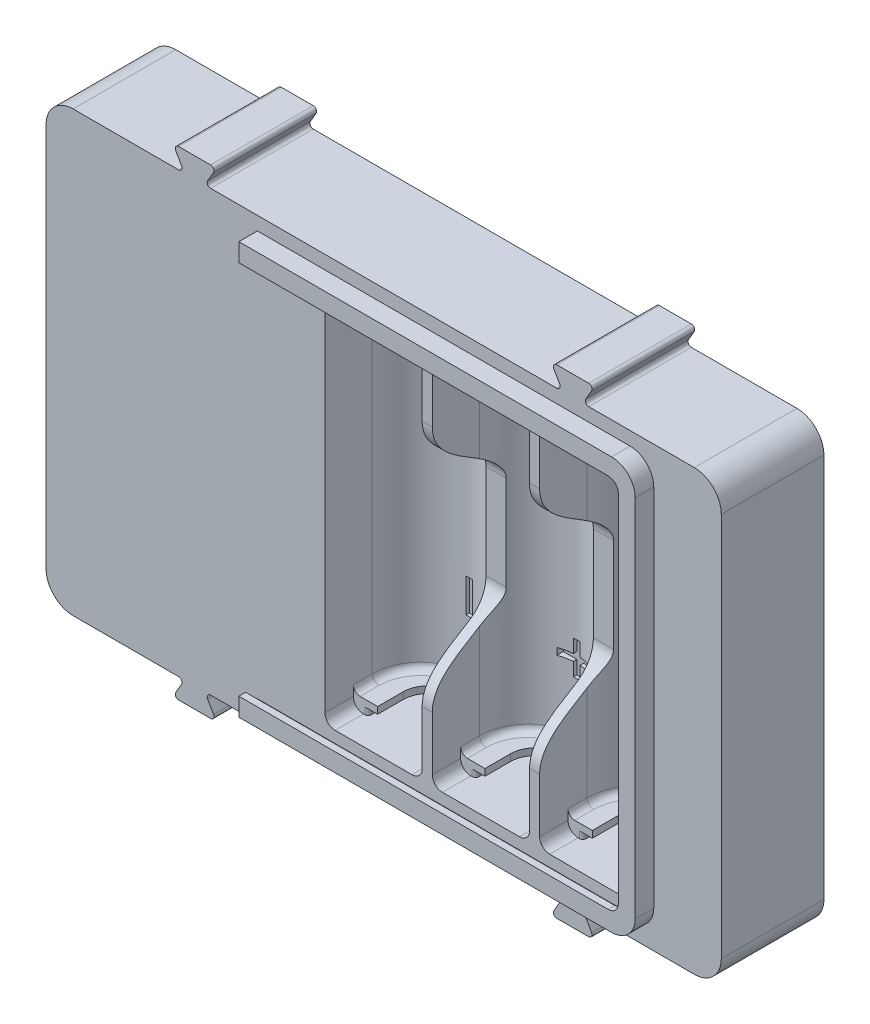
SolidWorks part; units mm, degrees
material "ABS"
ref_plane "Front Plane" through (0, 0, 0) normal (0, 0, 1) x (1, 0, 0)
ref_plane "Top Plane" through (0, 0, 0) normal (0, 1, 0) x (1, 0, 0)
ref_plane "Right Plane" through (0, 0, 0) normal (1, 0, 0) x (0, 0, -1)
sketch "Sketch1" plane through (0, 0, 0) normal (0, 1, 0) x (1, 0, 0)
  line L0 (-24.6, 0) -> (24.6, 0)
  line L1 (0, 0) -> (0, -8.2) construction
  line L2 (-5.4908, -1) -> (5.6475, -1) construction
  line L3 (7, -12.213) -> (7, -2.6204) construction
  line L4 (8.9, -12.0066) -> (8.9, -2.0587) construction
  line L5 (0, -8.2) -> (15.9, -8.2) construction
  line L6 (7.2, -8.2) -> (7.2, -15.2)
  line L7 (8.7, -8.2) -> (8.7, -15.2)
  line L8 (8.7, -15.2) -> (23.1, -15.2) construction
  line L9 (8.7, -15.2) -> (7.2, -15.2)
  line L10 (-1.7094, -15.2) -> (7.2, -15.2) construction
  line L11 (15.9, -8.2) -> (23.1, -8.2) construction
  line L12 (23.1, -15.2) -> (23.1, -8.2)
  line L13 (23.1, -15.2) -> (24.6, -15.2)
  line L14 (24.6, -15.2) -> (24.6, 0)
  line L15 (-24.6, -15.2) -> (-24.6, 0)
  line L16 (-23.1, -15.2) -> (-24.6, -15.2)
  line L17 (-23.1, -15.2) -> (-23.1, -8.2)
  line L18 (-8.7, -8.2) -> (-8.7, -15.2)
  line L19 (-8.7, -15.2) -> (-7.2, -15.2)
  line L20 (-7.2, -8.2) -> (-7.2, -15.2)
  circle A0 centre (0, -8.2) radius 7 construction
  arc A1 (-7.2, -8.2) -> (7.2, -8.2) centre (0, -8.2) cw
  circle A2 centre (15.9, -8.2) radius 7 construction
  arc A3 (8.7, -8.2) -> (23.1, -8.2) centre (15.9, -8.2) cw
  arc A4 (-8.7, -8.2) -> (-23.1, -8.2) centre (-15.9, -8.2) ccw
  dimension "D1" = 14
  dimension "D2" = 0.2
  dimension "D3" = 1
  dimension "D4" = 1.5
  dimension "D5" = 15.2
  dimension "D6" = 15.9
extrude "Boss-Extrude1" add sketch "Sketch1" along normal blind 27.8
sketch "Sketch2" plane through (0, 27.8, 0) normal (0, -1, 0) x (1, 0, 0)
  line L1 (-24.6, 15.2) -> (24.6, 15.2)
  line L2 (-24.6, 15.2) -> (-24.6, 0)
  line L3 (-24.6, 0) -> (24.6, 0)
  line L4 (24.6, 15.2) -> (24.6, 0)
extrude "Boss-Extrude2" add sketch "Sketch2" against normal blind 1.5
ref_plane "Plane1" through (-15.9, 0, 0) normal (1, 0, 0) x (0, 0, -1)
ref_plane "Plane3" through (15.9, 0, 0) normal (1, 0, 0) x (0, 0, -1)
sketch "Sketch6" plane through (0, 0, 0) normal (1, 0, 0) x (0, 0, -1)
  line L0 (-5, 0) -> (-15.2, 0)
  line L1 (-15.2, 0) -> (0, 0) construction
  line L2 (-15.2, 0) -> (-15.2, 18.3)
  line L3 (-15.2, 29.3) -> (-15.2, 0) construction
  line L4 (-5, 0) -> (-5, 7)
  line L5 (0, 29.3) -> (0, 0) construction
  line L6 (0, 29.3) -> (-15.2, 29.3) construction
  spline S0 degree 3 poles (-15.2, 18.3) (-15.2, 12.3) (-5, 11) (-5, 7) knots 0 0 0 0 1 1 1 1
  dimension "D4" = 12
  dimension "D5" = 18
  dimension "D1" = 7
  dimension "D2" = 5
  dimension "D3" = 11
extrude "Cut-Extrude2" cut sketch "Sketch6" against normal blind 15 and the other way blind 15
sketch "Sketch3" plane through (0, 27.8, 0) normal (0, -1, 0) x (1, 0, 0)
  line L0 (-10.4, 11) -> (-8.7, 11)
  line L1 (-8.7, 8.2) -> (-8.7, 15.2) construction
  line L2 (-8.7, 11) -> (-8.7, 0)
  line L3 (24.6, 0) -> (-24.6, 0) construction
  line L4 (-8.7, 0) -> (-23.1, 0)
  line L6 (-20.4, 2.9) -> (-11.4, 2.9)
  line L7 (-10.9, 3.4) -> (-10.9, 10.5)
  line L8 (-15.9, 15.2) -> (-15.9, 0) construction
  line L9 (-8.7, 15.2) -> (-23.1, 15.2) construction
  line L19 (-23.1, 11) -> (-23.1, 0)
  line L20 (-21.4, 11) -> (-23.1, 11)
  line L21 (-20.9, 3.4) -> (-20.9, 10.5)
  arc A1 (-11.4, 2.9) -> (-10.9, 3.4) centre (-11.4, 3.4) ccw
  arc A4 (-10.4, 11) -> (-10.9, 10.5) centre (-10.4, 10.5) ccw
  arc A6 (-20.4, 2.9) -> (-20.9, 3.4) centre (-20.4, 3.4) cw
  arc A7 (-21.4, 11) -> (-20.9, 10.5) centre (-21.4, 10.5) cw
  dimension "D6" = 0.5
  dimension "D7" = 0.5
  dimension "D1" = 5
  dimension "D2" = 11
  dimension "D3" = 2.9
extrude "Inner" add sketch "Sketch3" along normal blind 1
sketch "Sketch4" plane through (0, 26.8, 0) normal (0, -1, 0) x (1, 0, 0)
  line L1 (-8.7, 8.2) -> (-8.7, 15.2) construction
  line L2 (-8.7, 11) -> (-8.7, 0)
  line L3 (24.6, 0) -> (-24.6, 0) construction
  line L4 (-8.7, 0) -> (-23.1, 0)
  line L5 (-23.1, 0) -> (-23.1, 11)
  line L6 (-8.7, 11) -> (-10.4, 11) construction
  line L7 (-23.1, 11) -> (-19.5, 11)
  line L8 (-19.5, 11) -> (-19.5, 7.2)
  line L10 (-12.3, 7.2) -> (-12.3, 11)
  line L11 (-12.3, 11) -> (-8.7, 11)
  arc A0 (-19.5, 7.2) -> (-12.3, 7.2) centre (-15.9, 7.2) ccw
  dimension "D1" = 3.6
  dimension "D2" = 3.8
extrude "Boss-Extrude4" add sketch "Sketch4" along normal blind 1
sketch "Sketch5" plane through (0, 0, 15.2) normal (0, 0, 1) x (1, 0, 0)
  line L0 (-8.7, 27.8) -> (-23.1, 27.8) construction
  line L1 (-17.6, 27.8) -> (-14.2, 27.8)
  line L2 (-17.6, 27.8) -> (-17.6, 27.3)
  line L3 (-17.6, 27.3) -> (-14.2, 27.3)
  line L4 (-14.2, 27.8) -> (-14.2, 27.3)
  point P10 (-15.9, 27.8)
  dimension "D1" = 0.5
  dimension "D2" = 3.4
extrude "Cut-Extrude1" cut sketch "Sketch5" against normal through all
sketch "Sketch10" plane through (0, 0, 0) normal (0, 0, 1) x (1, 0, 0)
  line L0 (-24.6, 29.3) -> (24.6, 29.3) construction
  line L1 (-14.2, 27.3) -> (-17.6, 27.3)
  line L2 (-14.2, 27.3) -> (-14.2, 29.3)
  line L3 (-14.2, 29.3) -> (-17.6, 29.3)
  line L4 (-17.6, 27.3) -> (-17.6, 29.3)
extrude "Cut-Extrude6" cut sketch "Sketch10" along normal blind 0.6
mirror "Mirror1" about plane through (0, 0, 0) normal (1, 0, 0) of "Cut-Extrude6", "Inner", "Boss-Extrude4", "Cut-Extrude1"
ref_plane "Plane2" through (-7.95, 0, 0) normal (1, 0, 0) x (0, 0, -1)
mirror "Mirror2" about plane through (-7.95, 0, 0) normal (1, 0, 0) of "Cut-Extrude6", "Inner", "Boss-Extrude4", "Cut-Extrude1"
fillet "Fillet2" radius 1.5 6 edges at (-8.7, 27.8, 13.1) (-23.1, 27.8, 13.1) (23.1, 27.8, 13.1) (-7.2, 27.8, 13.1) (7.2, 27.8, 13.1) (8.7, 27.8, 13.1)
fillet "Fillet3" radius 1 9 edges at (-8.7, 25.8, 9.6) (-15.9, 25.8, 1) (-23.1, 25.8, 9.6) (23.1, 25.8, 9.6) (8.7, 25.8, 9.6) (7.2, 25.8, 9.6) (-7.2, 25.8, 9.6) (15.9, 25.8, 1) (0, 25.8, 1)
mirror "Mirror4" about plane through (0, 0, 0) normal (0, 1, 0) of bodies 108 110
sketch "Эскиз1" plane through (0, 0, 0) normal (0, 0, -1) x (-1, 0, 0)
  line L0 (-24.6, 29.3) -> (-24.6, -29.3) construction
  line L5 (-35.6, 32.5) -> (64.4, 32.5)
  line L6 (-35.6, 32.5) -> (-35.6, -32.5)
  line L7 (-35.6, -32.5) -> (64.4, -32.5)
  line L8 (64.4, 32.5) -> (64.4, -32.5)
  line L9 (-35.6, 32.5) -> (64.4, -32.5) construction
  line L10 (-35.6, -32.5) -> (64.4, 32.5) construction
  line L11 (-34.6, -31.5) -> (63.4, -31.5)
  line L12 (-34.6, -31.5) -> (-34.6, 31.5)
  line L13 (-34.6, 31.5) -> (63.4, 31.5)
  line L14 (63.4, -31.5) -> (63.4, 31.5)
  line L15 (-34.6, -31.5) -> (63.4, 31.5) construction
  line L16 (-34.6, 31.5) -> (63.4, -31.5) construction
  line L17 (24.6, 29.3) -> (24.6, -29.3) construction
  line L18 (-24.6, 29.3) -> (24.6, 29.3)
  line L19 (-24.6, 29.3) -> (-24.6, 31.5)
  line L20 (-24.6, 31.5) -> (24.6, 31.5)
  line L21 (24.6, 29.3) -> (24.6, 31.5)
  line L22 (-24.6, -29.3) -> (24.6, -29.3)
  line L23 (-24.6, -29.3) -> (-24.6, -31.5)
  line L24 (-24.6, -31.5) -> (24.6, -31.5)
  line L25 (24.6, -29.3) -> (24.6, -31.5)
  line L27 (-24.6, 29.3) -> (-24.6, -29.3) construction
  line L28 (63.4, 31.5) -> (55.9, 31.5)
  line L29 (63.4, 31.5) -> (63.4, 24)
  line L30 (63.4, 24) -> (55.9, 24)
  line L31 (55.9, 31.5) -> (55.9, 24)
  line L32 (63.4, -31.5) -> (55.9, -31.5)
  line L33 (63.4, -31.5) -> (63.4, -24)
  line L34 (63.4, -24) -> (55.9, -24)
  line L35 (55.9, -31.5) -> (55.9, -24)
  line L36 (-34.6, 31.5) -> (-24.6, 31.5)
  line L37 (-34.6, 31.5) -> (-34.6, 24)
  line L38 (-34.6, 24) -> (-24.6, 24)
  line L39 (-24.6, 31.5) -> (-24.6, 24)
  line L41 (-34.6, -31.5) -> (-24.6, -31.5)
  line L42 (-34.6, -31.5) -> (-34.6, -24)
  line L43 (-34.6, -24) -> (-24.6, -24)
  line L44 (-24.6, -31.5) -> (-24.6, -24)
  point P0 (14.4, 0)
  point P5 (14.4, 0)
  line M16 (24.6, 29.3) -> (17.6, 29.3)
  line M20 (14.2, 29.3) -> (1.7, 29.3)
  line M24 (-1.7, 29.3) -> (-14.2, 29.3)
  line M28 (-17.6, 29.3) -> (-24.6, 29.3)
  line M30 (-24.6, 29.3) -> (-24.6, -29.3)
  dimension "D1" = 100
  dimension "D2" = 65
  dimension "D3" = 1
  dimension "D4" = 1
  dimension "D5" = 10
  dimension "D6" = 7.5
extrude "Бобышка-Вытянуть1" add sketch "Эскиз1" against normal up to surface (15.2 mm away) contours L13 L31 L30 L14 | L35 L11 L14 L34 | L43 L12 L11 L23 M30 | L12 L38 L19 L13 M30 | L8 L5 L6 L7 L14 L11 L12 L13 | L21 L13 L19 L18 M16 M28 M24 M20
sketch "Эскиз2" plane through (0, 0, 0) normal (0, 0, -1) x (-1, 0, 0)
  line L0 (63.4, -24) -> (63.4, 24) construction
  line L1 (-34.6, -31.5) -> (63.4, -31.5)
  line L2 (-34.6, -31.5) -> (-34.6, 31.5)
  line L3 (-34.6, 31.5) -> (63.4, 31.5)
  line L4 (63.4, -31.5) -> (63.4, 31.5)
  line L5 (-34.6, -24) -> (-34.6, 24) construction
  line L6 (24.6, 31.5) -> (55.9, 31.5) construction
  line L7 (24.6, -31.5) -> (55.9, -31.5) construction
  line L11 (-34.6, 24) -> (-27.1, 24)
  line L12 (-27.1, 31.5) -> (-27.1, 24)
  line L13 (55.9, 24) -> (63.4, 24)
  line L14 (55.9, 24) -> (55.9, 31.5)
  line L17 (55.9, -24) -> (63.4, -24)
  line L18 (55.9, -24) -> (55.9, -31.5)
  line L23 (-34.6, -24) -> (-27.1, -24)
  line L24 (-27.1, -31.5) -> (-27.1, -24)
  line L25 (-27.1, 29.5) -> (55.9, 29.5)
  line L26 (-27.1, -29.5) -> (55.9, -29.5)
  line L27 (-33.6, 24) -> (-33.6, -24)
  line L28 (62.4, -24) -> (62.4, 24)
  line L29 (63.4, 24) -> (55.9, 24) construction
  line L30 (-34.6, -24) -> (-24.6, -24) construction
  line M29 (24.6, -31.5) -> (24.6, 31.5)
  dimension "D1" = 1
  dimension "D2" = 1
  dimension "D3" = 2
  dimension "D4" = 2
  dimension "D5" = 7.5
extrude "Вырез-Вытянуть5" cut sketch "Эскиз2" against normal blind 2 contours L26 L24 L1 M29 | L12 L25 L3 M29
sketch "Эскиз11" plane through (0, 0, 15.2) normal (0, 0, 1) x (1, 0, 0)
  line L0 (-43.9, 32.5) -> (-45.6321, 35.5)
  line L2 (-45.6321, 35.5) -> (-39.1679, 35.5)
  line L3 (-39.1679, 35.5) -> (-40.9, 32.5)
  line L4 (-40.9, 32.5) -> (-43.9, 32.5)
  line L5 (12.1, 32.5) -> (10.3679, 35.5)
  line L6 (10.3679, 35.5) -> (16.8321, 35.5)
  line L7 (16.8321, 35.5) -> (15.1, 32.5)
  line L8 (15.1, 32.5) -> (12.1, 32.5)
  line L11 (-43.9, -32.5) -> (-45.6321, -35.5)
  line L13 (-45.6321, -35.5) -> (-39.1679, -35.5)
  line L14 (-39.1679, -35.5) -> (-40.9, -32.5)
  line L15 (-40.9, -32.5) -> (-43.9, -32.5)
  line L16 (12.1, -32.5) -> (10.3679, -35.5)
  line L17 (10.3679, -35.5) -> (16.8321, -35.5)
  line L18 (16.8321, -35.5) -> (15.1, -32.5)
  line L19 (15.1, -32.5) -> (12.1, -32.5)
  line L20 (-64.4, -32.5) -> (35.6, -32.5) construction
  line L21 (-64.4, 32.5) -> (35.6, 32.5) construction
  line L22 (-64.4, -32.5) -> (-64.4, 32.5) construction
  line L23 (35.6, -32.5) -> (35.6, 32.5) construction
  dimension "D1" = 60
  dimension "D2" = 3
  dimension "D3" = 3
  dimension "D4" = 3
  dimension "D5" = 20.5
  dimension "D6" = 20.5
  dimension "D7" = 3
extrude "Бобышка-Вытянуть3" add sketch "Эскиз11" against normal up to surface (15.2 mm away) up to face at (-15.9, 28.3, 0)
fillet "Скругление8" radius 0.5 16 edges at (-45.6321, -35.5, 7.6) (-43.9, -32.5, 7.6) (-39.1679, -35.5, 7.6) (-40.9, -32.5, 7.6) (16.8321, -35.5, 7.6) (15.1, -32.5, 7.6) (10.3679, -35.5, 7.6) (12.1, -32.5, 7.6) (15.1, 32.5, 7.6) (16.8321, 35.5, 7.6) (12.1, 32.5, 7.6) (10.3679, 35.5, 7.6) (-43.9, 32.5, 7.6) (-40.9, 32.5, 7.6) (-39.1679, 35.5, 7.6) (-45.6321, 35.5, 7.6)
sketch "Эскиз12" plane through (0, 0, 0) normal (0, 0, -1) x (-1, 0, 0)
  line L4 (-35.6, 32.5) -> (-35.6, -32.5) construction
  line L6 (64.4, 32.5) -> (64.4, -32.5) construction
  line L7 (44.766, -32.5) -> (64.4, -32.5) construction
  line L8 (-35.6, 32.5) -> (-15.966, 32.5) construction
  circle A0 centre (-31.1, 28) radius 1.9
  circle A1 centre (59.9, 28) radius 1.9
  circle A2 centre (59.9, -28) radius 1.9
  circle A3 centre (-31.1, -28) radius 1.9
  point P8 (59.9, 28)
  point P9 (59.9, -28)
  point P10 (-31.1, -28)
  point P12 (-31.1, 28)
  dimension "D1" = 3.8
  dimension "D2" = 4.5
  dimension "D3" = 4.5
  dimension "D4" = 4.5
  dimension "D5" = 4.5
extrude "Вырез-Вытянуть2" cut sketch "Эскиз12" against normal blind 5
fillet "Скругление10" radius 4 2 edges at (-55.9, 24, 7.6) (-55.9, -24, 7.6)
sketch "Эскиз13" [suppressed] plane through (0, 0, 15.2) normal (0, 0, 1) x (1, 0, 0)
  line L1 (-24.6, 31.5) -> (27.1, 31.5)
  line L2 (-24.6, 31.5) -> (-24.6, -31.5)
  line L3 (-24.6, -31.5) -> (27.1, -31.5)
  line L4 (27.1, 31.5) -> (27.1, -31.5)
  line L5 (-55.9, -31.5) -> (-24.6, -31.5) construction
  line L6 (-55.9, 31.5) -> (-24.6, 31.5) construction
  line L8 (34.6, 24) -> (34.6, -24) construction
  line L9 (-24.6, 31.5) -> (-24.6, -31.5) construction
  dimension "D1" = 7.5
extrude "Вырез-Вытянуть4" [suppressed] cut sketch "Эскиз13" against normal through all
sketch "Эскиз17" plane through (0, 0, 15.2) normal (0, 0, 1) x (1, 0, 0)
  line L0 (-40.034, -32.5) -> (11.234, -32.5) construction
  line L1 (-64.4, 32.5) -> (-24.6, 32.5)
  line L2 (-64.4, 32.5) -> (-64.4, -32.5)
  line L3 (-64.4, -32.5) -> (-24.6, -32.5)
  line L4 (-24.6, 32.5) -> (-24.6, -32.5)
  line L6 (35.6, -32.5) -> (24.6, -32.5)
  line L7 (35.6, -32.5) -> (35.6, 32.5)
  line L8 (35.6, 32.5) -> (24.6, 32.5)
  line L9 (24.6, -32.5) -> (24.6, 32.5)
  line L12 (15.966, 32.5) -> (35.6, 32.5) construction
  dimension "D1" = 39.8
  dimension "D2" = 11
extrude "Бобышка-Вытянуть4" add sketch "Эскиз17" against normal blind 1
sketch "Эскиз24" [suppressed] plane through (0, 0, 15.2) normal (0, 0, 1) x (1, 0, 0)
  line L1 (-64.4, 32.5) -> (35.6, 32.5)
  line L2 (-64.4, 32.5) -> (-64.4, -32.5)
  line L3 (-64.4, -32.5) -> (35.6, -32.5)
  line L4 (35.6, 32.5) -> (35.6, -32.5)
extrude "Бобышка-Вытянуть7" [suppressed] add sketch "Эскиз24" against normal blind 1
fillet "Скругление13" radius 4 4 edges at (-64.4, 32.5, 7.6) (35.6, 32.5, 7.6) (35.6, -32.5, 7.6) (-64.4, -32.5, 7.6)
sketch "Эскиз18" plane through (0, 0, 0) normal (0, 0, -1) x (-1, 0, 0)
  line L1 (-17.6, 27.3) -> (-14.2, 27.3)
  line L2 (-17.6, 27.3) -> (-17.6, 29.5)
  line L3 (-17.6, 29.5) -> (-14.2, 29.5)
  line L4 (-14.2, 27.3) -> (-14.2, 29.5)
  line L5 (-27.1, 29.5) -> (24.6, 29.5) construction
  line L6 (-1.7, 27.3) -> (1.7, 27.3)
  line L7 (-1.7, 27.3) -> (-1.7, 29.5)
  line L8 (-1.7, 29.5) -> (1.7, 29.5)
  line L9 (1.7, 27.3) -> (1.7, 29.5)
  line L10 (14.2, 27.3) -> (17.6, 27.3)
  line L11 (14.2, 27.3) -> (14.2, 29.5)
  line L12 (14.2, 29.5) -> (17.6, 29.5)
  line L13 (17.6, 27.3) -> (17.6, 29.5)
  line L14 (-27.1, -29.5) -> (24.6, -29.5) construction
  line L15 (14.2, -27.3) -> (17.6, -27.3)
  line L16 (14.2, -27.3) -> (14.2, -29.5)
  line L17 (14.2, -29.5) -> (17.6, -29.5)
  line L18 (17.6, -27.3) -> (17.6, -29.5)
  line L19 (-27.1, -29.5) -> (24.6, -29.5) construction
  line L20 (-1.7, -27.3) -> (1.7, -27.3)
  line L21 (-1.7, -27.3) -> (-1.7, -29.5)
  line L22 (-1.7, -29.5) -> (1.7, -29.5)
  line L23 (1.7, -27.3) -> (1.7, -29.5)
  line L24 (-17.6, -27.3) -> (-14.2, -27.3)
  line L25 (-17.6, -27.3) -> (-17.6, -29.5)
  line L26 (-17.6, -29.5) -> (-14.2, -29.5)
  line L27 (-14.2, -27.3) -> (-14.2, -29.5)
  line L28 (1.7, -27.3) -> (1.7, -29.3) construction
  line L29 (-14.2, -27.3) -> (-14.2, -29.3) construction
  line L30 (17.6, -29.3) -> (17.6, -27.3) construction
  line L31 (17.6, 29.3) -> (17.6, 27.8) construction
  line L32 (1.7, 27.8) -> (1.7, 29.3) construction
  line L33 (-14.2, 27.8) -> (-14.2, 29.3) construction
  line L35 (-27.1, 29.5) -> (24.6, 29.5) construction
  line L36 (-27.1, 29.5) -> (24.6, 29.5) construction
extrude "Вырез-Вытянуть6" cut sketch "Эскиз18" against normal up to surface (2 mm away) up to face at (1.25, -30.5, 2)
sketch "Эскиз20" plane through (0, 0, 15.2) normal (0, 0, 1) x (1, 0, 0)
  line L0 (-64.4, -28.5) -> (-64.4, 28.5) construction
  line L5 (-18.4, 15.5) -> (-13.4, 15.5)
  line L6 (-18.4, 15.5) -> (-18.4, 14.5)
  line L7 (-18.4, 14.5) -> (-13.4, 14.5)
  line L8 (-13.4, 15.5) -> (-13.4, 14.5)
  line L9 (-18.4, 15.5) -> (-13.4, 14.5) construction
  line L10 (-18.4, 14.5) -> (-13.4, 15.5) construction
  line L11 (-16.4, 17.5) -> (-15.4, 17.5)
  line L12 (-16.4, 17.5) -> (-16.4, 12.5)
  line L13 (-16.4, 12.5) -> (-15.4, 12.5)
  line L14 (-15.4, 17.5) -> (-15.4, 12.5)
  line L15 (-16.4, 17.5) -> (-15.4, 12.5) construction
  line L16 (-16.4, 12.5) -> (-15.4, 17.5) construction
  line L17 (-16.4, -12.5) -> (-15.4, -12.5)
  line L18 (-16.4, -12.5) -> (-16.4, -17.5)
  line L19 (-16.4, -17.5) -> (-15.4, -17.5)
  line L20 (-15.4, -12.5) -> (-15.4, -17.5)
  line L21 (-16.4, -12.5) -> (-15.4, -17.5) construction
  line L22 (-16.4, -17.5) -> (-15.4, -12.5) construction
  line L23 (-10.2, 27.8) -> (-21.6, 27.8) construction
  line L24 (5.7, 27.8) -> (-5.7, 27.8) construction
  line L25 (21.6, 27.8) -> (10.2, 27.8) construction
  line L43 (-0.5, 12.5) -> (0.5, 12.5)
  line L44 (-0.5, 12.5) -> (-0.5, 17.5)
  line L45 (-0.5, 17.5) -> (0.5, 17.5)
  line L46 (0.5, 12.5) -> (0.5, 17.5)
  line L47 (-0.5, 12.5) -> (0.5, 17.5) construction
  line L48 (-0.5, 17.5) -> (0.5, 12.5) construction
  line L49 (15.4, 12.5) -> (16.4, 12.5)
  line L50 (15.4, 12.5) -> (15.4, 17.5)
  line L51 (15.4, 17.5) -> (16.4, 17.5)
  line L52 (16.4, 12.5) -> (16.4, 17.5)
  line L53 (15.4, 12.5) -> (16.4, 17.5) construction
  line L54 (15.4, 17.5) -> (16.4, 12.5) construction
  line L55 (15.4, -17.5) -> (16.4, -17.5)
  line L56 (15.4, -17.5) -> (15.4, -12.5)
  line L57 (15.4, -12.5) -> (16.4, -12.5)
  line L58 (16.4, -17.5) -> (16.4, -12.5)
  line L59 (15.4, -17.5) -> (16.4, -12.5) construction
  line L60 (15.4, -12.5) -> (16.4, -17.5) construction
  line L61 (-0.5, -17.5) -> (0.5, -17.5)
  line L62 (-0.5, -17.5) -> (-0.5, -12.5)
  line L63 (-0.5, -12.5) -> (0.5, -12.5)
  line L64 (0.5, -17.5) -> (0.5, -12.5)
  line L65 (-0.5, -17.5) -> (0.5, -12.5) construction
  line L66 (-0.5, -12.5) -> (0.5, -17.5) construction
  line L67 (13.4, 14.5) -> (18.4, 14.5)
  line L68 (13.4, 14.5) -> (13.4, 15.5)
  line L69 (13.4, 15.5) -> (18.4, 15.5)
  line L70 (18.4, 14.5) -> (18.4, 15.5)
  line L71 (13.4, 14.5) -> (18.4, 15.5) construction
  line L72 (13.4, 15.5) -> (18.4, 14.5) construction
  line L73 (-2.5, -15.5) -> (2.5, -15.5)
  line L74 (-2.5, -15.5) -> (-2.5, -14.5)
  line L75 (-2.5, -14.5) -> (2.5, -14.5)
  line L76 (2.5, -15.5) -> (2.5, -14.5)
  line L77 (-2.5, -15.5) -> (2.5, -14.5) construction
  line L78 (-2.5, -14.5) -> (2.5, -15.5) construction
  point P0 (-15.9, -15)
  point P4 (-15.9, 15)
  point P9 (-15.9, 15)
  point P15 (15.9, 27.8)
  point P16 (-15.9, 27.8)
  point P17 (0, 15)
  point P18 (-15.9, 0)
  point P22 (-64.4, 0)
  point P24 (0, 27.8)
  point P33 (15.9, 15)
  point P38 (15.9, -15)
  point P43 (0, -15)
  point P48 (0, -15)
  point P52 (15.9, 15)
  dimension "D1" = 1
  dimension "D2" = 5
  dimension "D3" = 15
  dimension "D4" = 15
extrude "Вырез-Вытянуть8" cut sketch "Эскиз20" against normal blind 14.7 contours L5 L8 L7 L6 | L14 L13 L12 L11 | L46 L45 L44 L43 | L69 L70 L67 L68 | L50 L51 L52 L49 | L56 L57 L58 L55 | L75 L76 L73 L74 | L62 L63 L64 L61 | L20 L19 L18 L17
sketch "Эскиз22" plane through (0, 0, 15.2) normal (0, 0, 1) x (1, 0, 0)
  line L0 (23.1, 24.8) -> (23.1, -24.8) construction
  line L1 (-33.1, 29.5) -> (24.6, 29.5)
  line L3 (-33.1, -29.5) -> (24.6, -29.5)
  line L4 (24.6, 29.5) -> (24.6, -29.5)
  line L8 (-33.1, -29.5) -> (-33.1, -30.5)
  line L9 (-33.1, 30.5) -> (25.6, 30.5)
  line L10 (-33.1, 30.5) -> (-33.1, 29.5)
  line L11 (-33.1, -30.5) -> (25.6, -30.5)
  line L12 (25.6, 30.5) -> (25.6, -30.5)
  line L13 (-23.1, 26.3) -> (-23.1, -26.3) construction
  dimension "D1" = 1.5
  dimension "D2" = 29.5
  dimension "D3" = 29.5
  dimension "D4" = 10
  dimension "D5" = 1
  dimension "D6" = 1
  dimension "D7" = 1
extrude "Бобышка-Вытянуть5" add sketch "Эскиз22" along normal blind 1.75
sketch "Эскиз23" plane through (0, 0, 16.95) normal (0, 0, 1) x (1, 0, 0)
  line L0 (-33.1, 30.5) -> (-33.1, 27.8)
  line L1 (-33.1, 27.8) -> (23.1, 27.8)
  line L2 (23.1, 27.8) -> (23.1, -27.8)
  line L3 (23.1, -27.8) -> (-33.1, -27.8)
  line L4 (-33.1, -27.8) -> (-33.1, -30.5)
  line L5 (-33.1, -30.5) -> (25.6, -30.5)
  line L6 (25.6, -30.5) -> (25.6, 30.5)
  line L7 (25.6, 30.5) -> (-33.1, 30.5)
  line L8 (23.1, 26.3) -> (23.1, -26.3) construction
  line L9 (5.7, 27.8) -> (-5.7, 27.8) construction
  line L10 (-10.2, -27.8) -> (-21.6, -27.8) construction
extrude "Бобышка-Вытянуть6" add sketch "Эскиз23" along normal blind 1
fillet "Скругление14" radius 2.5 2 edges at (24.6, -29.5, 16.075) (24.6, 29.5, 16.075)
fillet "Скругление15" radius 3.5 2 edges at (25.6, -30.5, 16.575) (25.6, 30.5, 16.575)
fillet "Скругление16" radius 1.5 2 edges at (23.1, -27.8, 17.45) (23.1, 27.8, 17.45)
fillet "Скругление17" [suppressed] radius 4
